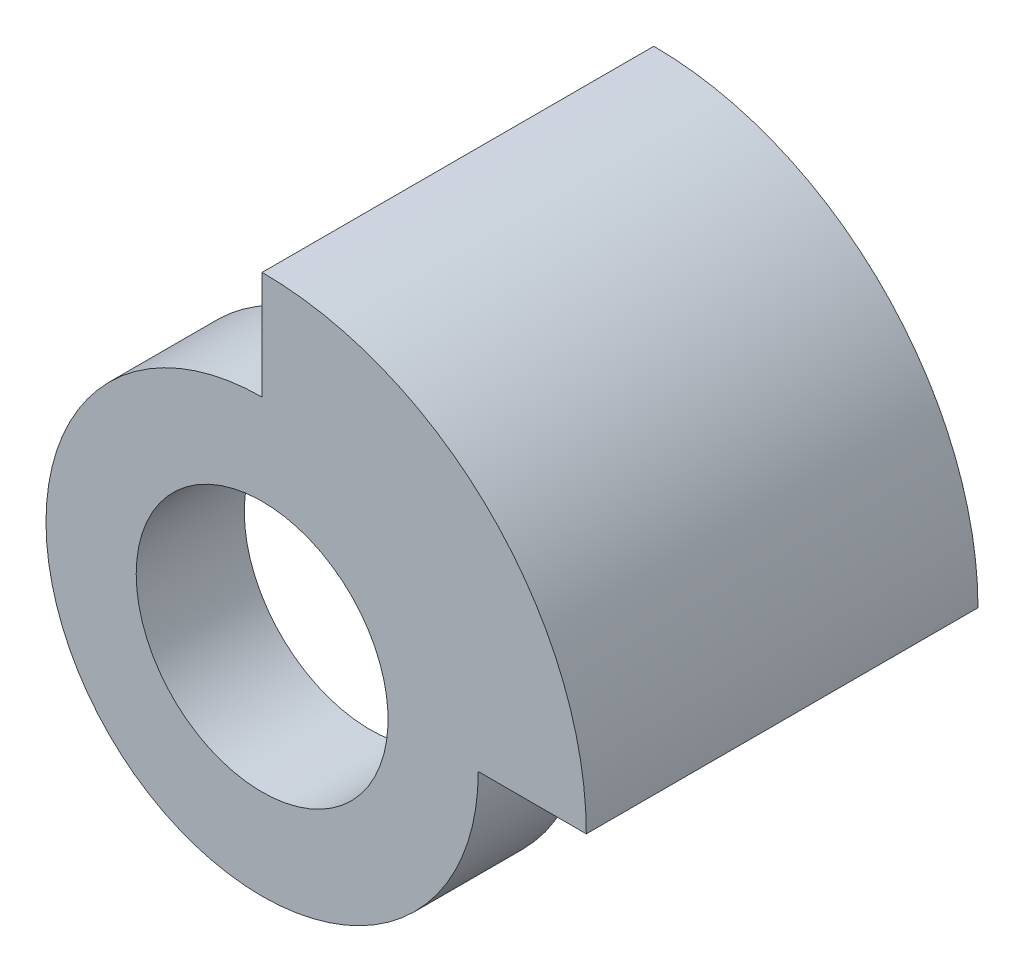
SolidWorks part; units mm, degrees
ref_plane "Front Plane" through (0, 0, 0) normal (0, 0, 1) x (1, 0, 0)
ref_plane "Top Plane" through (0, 0, 0) normal (0, 1, 0) x (1, 0, 0)
ref_plane "Right Plane" through (0, 0, 0) normal (1, 0, 0) x (0, 0, -1)
sketch "Sketch1" plane through (0, 0, 0) normal (0, 0, 1) x (1, 0, 0)
  line L0 (0, 28.575) -> (0, 19.0514)
  line L1 (28.575, 0) -> (19.0514, 0)
  line L2 (0, 0) -> (18.0981, 18.0981) construction
  line L3 (13.4704, 13.4704) -> (13.4714, 13.4714)
  circle A0 centre (0, 0) radius 19.0514
  circle A1 centre (0, 0) radius 11.1
  arc A2 (0, 28.575) -> (28.575, 0) centre (0, 0) cw
  spline S0 degree 2 poles (0, 28.575) (21.9087, 21.9087) (28.575, 0) knots 0 0 0 1 1 1
  point P13 (0, 0)
  dimension "D2" = 22.2
extrude "Boss-Extrude5" add sketch "Sketch1" along normal blind 9.525
sketch "Sketch2" plane through (0, 0, 0) normal (0, 0, -1) x (-1, 0, 0)
  line L0 (0, 28.575) -> (0, 19.0514) construction
  line L1 (-28.575, 0) -> (-19.0514, 0) construction
  line L2 (0, 28.575) -> (0, 19.4)
  line L3 (-28.575, 0) -> (-19.4, 0)
  arc A0 (0, 19.4) -> (-19.4, 0) centre (0, 0) ccw
  parabola Q1 (0, 28.575) -> (-28.575, 0) focus (-4.7056, 4.7056) apex (-18.0981, 18.0981)
  line M2 (-28.575, 0) -> (-19.0514, 0)
  line M4 (0, 19.0514) -> (0, 28.575)
  arc M10 (0, 28.575) -> (-28.575, 0) centre (0, 0) ccw
extrude "Boss-Extrude6" add sketch "Sketch2" along normal blind 25 contours Q1 M10 | Q1 A0 M4 M2
